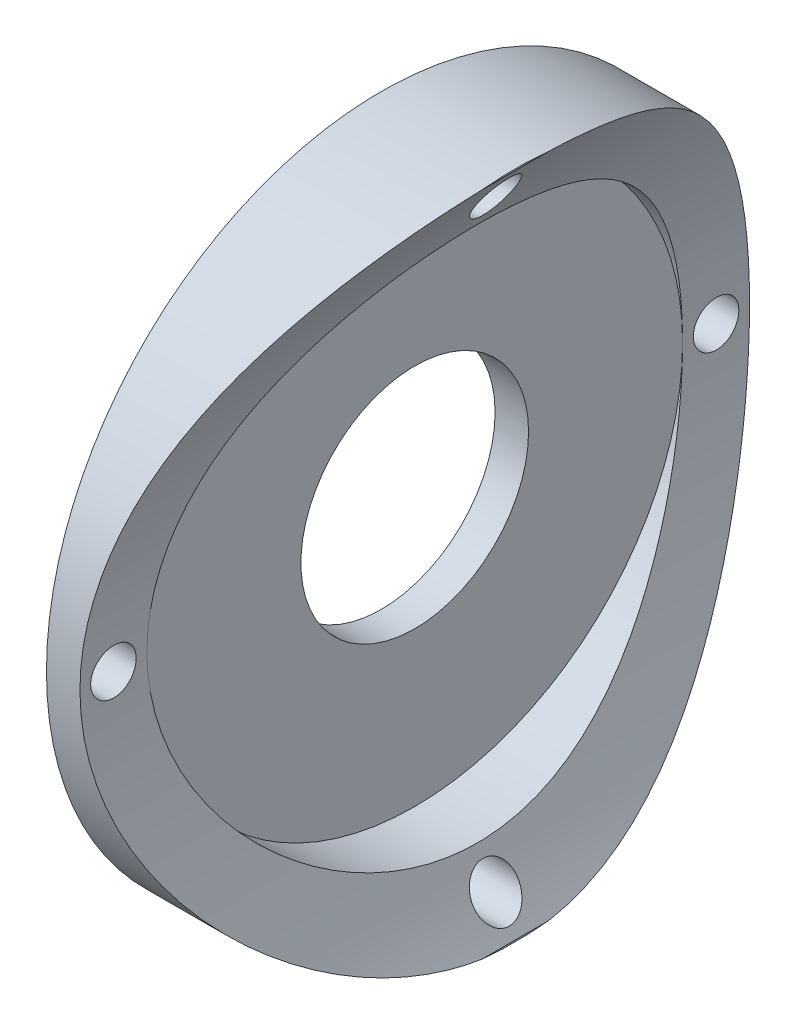
SolidWorks part; units mm, degrees
ref_plane "Front Plane" through (0, 0, 0) normal (0, 0, 1) x (1, 0, 0)
ref_plane "Top Plane" through (0, 0, 0) normal (0, 1, 0) x (1, 0, 0)
ref_plane "Right Plane" through (0, 0, 0) normal (1, 0, 0) x (0, 0, -1)
sketch "Sketch2" plane through (0, 0, 0) normal (1, 0, 0) x (0, 0, -1)
  circle A0 centre (0, 0) radius 8.5
  circle A1 centre (0, 0) radius 25
extrude "Boss-Extrude1" add sketch "Sketch2" along normal blind 10
sketch "Sketch3" plane through (0, 0, 0) normal (0, 0, 1) x (1, 0, 0)
  line L0 (0, 0) -> (2.5, 0) construction
  line L1 (2.5, 0) -> (47.5, 0) construction
  circle A0 centre (47.5, 0) radius 45
extrude "Cut-Extrude3" cut sketch "Sketch3" against normal blind 28 and the other way blind 29 contours A0
sketch "Sketch5" plane through (10, 0, 0) normal (1, 0, 0) x (0, 0, -1)
  circle A0 centre (0, 0) radius 20
extrude "Cut-Extrude4" cut sketch "Sketch5" against normal blind 7.5
sketch "Sketch6" plane through (0, 0, 0) normal (-1, 0, 0) x (0, 0, 1)
  circle A0 centre (0, 0) radius 22.5 construction
hole_wizard "M3 Clearance Hole1" positions "Sketch10" profile "Sketch8" hole size "M3" standard "IS"
sketch "Sketch10" plane through (0, 0, 0) normal (-1, 0, 0) x (0, 0, 1)
  circle A0 centre (0, 0) radius 22.5 construction
  point P0 (22.5, 0)
  point P4 (0, 22.5)
  point P6 (-22.5, 0)
  point P8 (0, -22.5)
sketch "Sketch8" plane through (0, 0, 22.5) normal (0, 1, 0) x (0, 0, 1)
  line L0 (0, 0) -> (0, 71.0215)
  line L1 (0, 71.0215) -> (1.7, 70)
  line L2 (1.7, 70) -> (1.7, 0)
  line L5 (1.7, 0) -> (0, 0)
  line L10 (0, 71.0215) -> (-1.7, 70) construction
  line L11 (0, -6.35) -> (0, 107.95) construction
  dimension "Hole Dia." = 3.4
  dimension "Hole Depth" = 70
  dimension "Drill Angle" = 118
